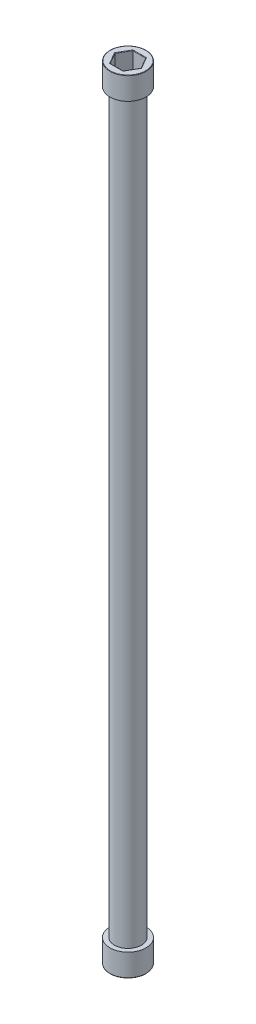
SolidWorks part; units mm, degrees
ref_plane "Front Plane" through (0, 0, 0) normal (0, 0, 1) x (1, 0, 0)
ref_plane "Top Plane" through (0, 0, 0) normal (0, 1, 0) x (1, 0, 0)
ref_plane "Right Plane" through (0, 0, 0) normal (1, 0, 0) x (0, 0, -1)
sketch "Sketch2" plane through (0, 0, 0) normal (0, 1, 0) x (1, 0, 0)
  circle A0 centre (0, 0) radius 3
  dimension "D1" = 6
extrude "Boss-Extrude1" add sketch "Sketch2" along normal mid plane 163
sketch "Sketch4" plane through (0, 81.5, 0) normal (0, 1, 0) x (1, 0, 0)
  circle A0 centre (0, 0) radius 4
  dimension "D1" = 8
extrude "Boss-Extrude2" add sketch "Sketch4" along normal blind 5
sketch "Sketch5" plane through (0, 86.5, 0) normal (0, 1, 0) x (1, 0, 0)
  line L1 (1.4434, -2.5) -> (2.8868, 0)
  line L2 (2.8868, 0) -> (1.4434, 2.5)
  line L3 (1.4434, 2.5) -> (-1.4434, 2.5)
  line L4 (-1.4434, 2.5) -> (-2.8868, 0)
  line L5 (-2.8868, 0) -> (-1.4434, -2.5)
  line L6 (-1.4434, -2.5) -> (1.4434, -2.5)
  circle A0 centre (0, 0) radius 2.5 construction
  dimension "D1" = 5
extrude "Cut-Extrude1" cut sketch "Sketch5" against normal blind 4
fillet "Fillet1" radius 0.1 13 edges at (0, 82.5, -2.5) (-2.1651, 82.5, -1.25) (-2.1651, 82.5, 1.25) (0, 82.5, 2.5) (2.1651, 82.5, 1.25) (2.1651, 82.5, -1.25) (0, 86.5, 4) (0, 86.5, 2.5) (-2.1651, 86.5, 1.25) (-2.1651, 86.5, -1.25) (0, 86.5, -2.5) (2.1651, 86.5, -1.25) (2.1651, 86.5, 1.25)
mirror "Mirror1" about plane through (0, 0, 0) normal (0, 1, 0) of "Fillet1", "Cut-Extrude1", "Boss-Extrude2"
